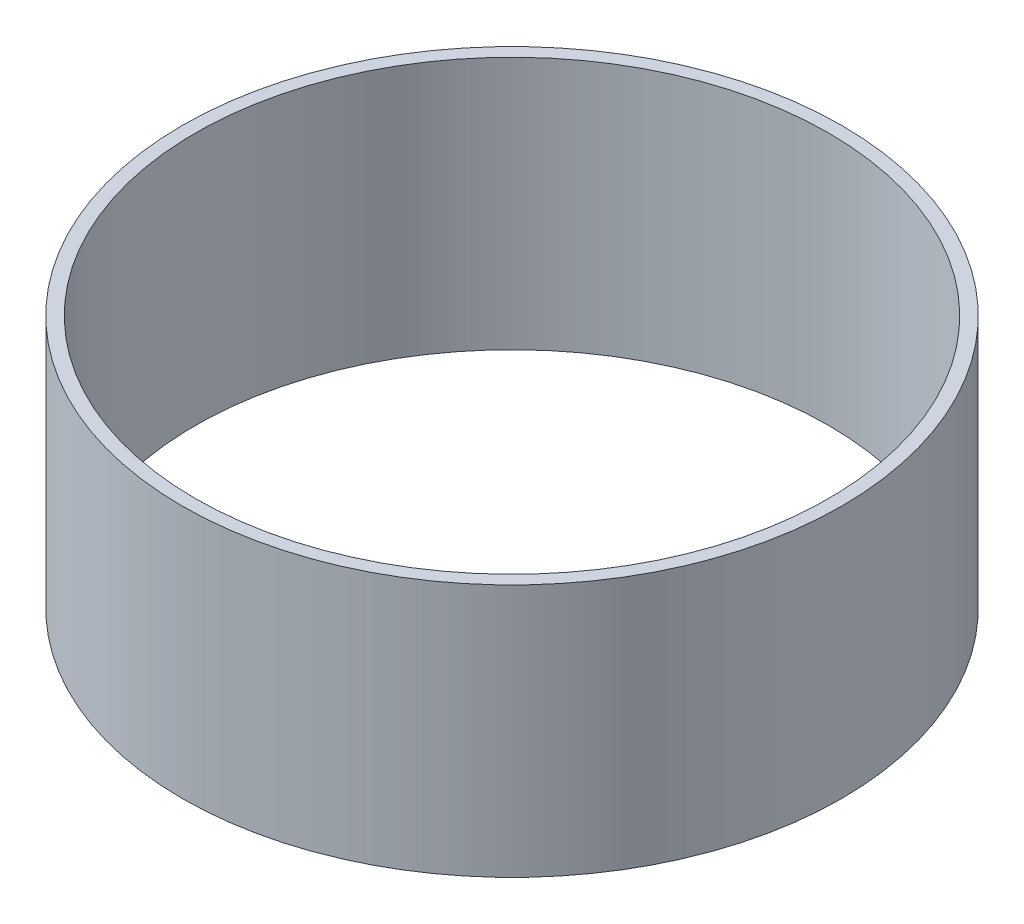
SolidWorks part; units mm, degrees
ref_plane "Front Plane" through (0, 0, 0) normal (0, 0, 1) x (1, 0, 0)
ref_plane "Top Plane" through (0, 0, 0) normal (0, 1, 0) x (1, 0, 0)
ref_plane "Right Plane" through (0, 0, 0) normal (1, 0, 0) x (0, 0, -1)
sketch "Sketch1" plane through (0, 0, 0) normal (0, 1, 0) x (1, 0, 0)
  circle A0 centre (0, 0) radius 39.6748
  circle A1 centre (0, 0) radius 38.1
  point P2 (0, 0)
  dimension "D1" = 79.3496
  dimension "D2" = 76.2
extrude "Boss-Extrude1" add sketch "Sketch1" along normal mid plane 30.48
